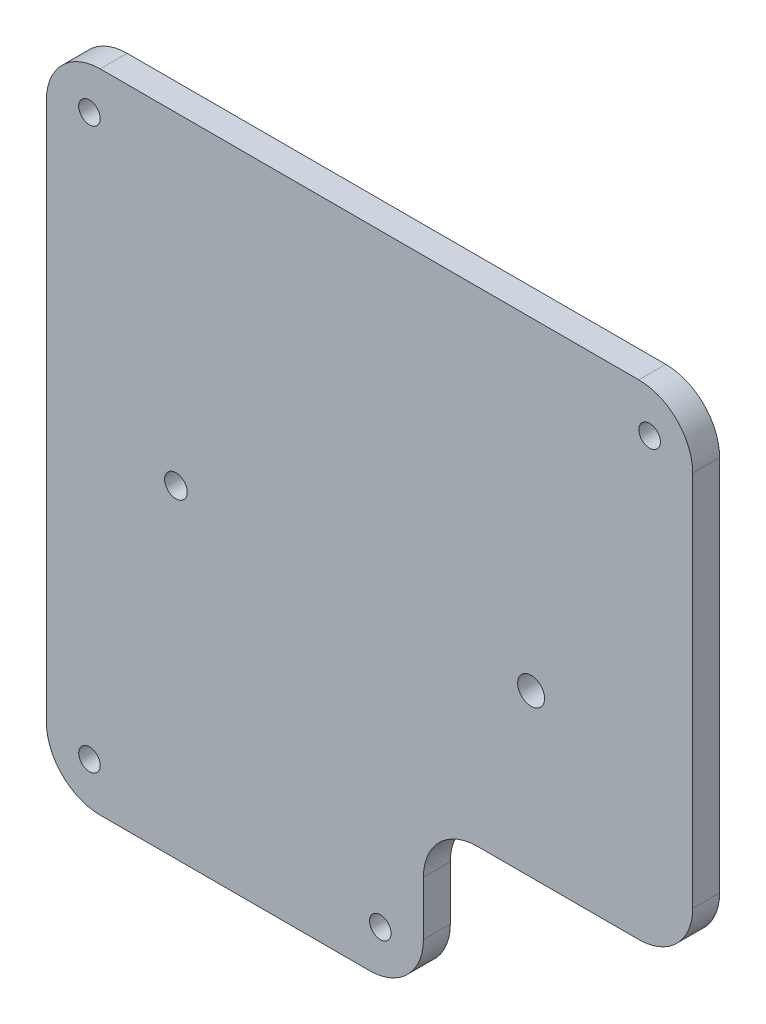
SolidWorks part; units mm, degrees
ref_plane "Alzado" through (0, 0, 0) normal (0, 0, 1) x (1, 0, 0)
ref_plane "Planta" through (0, 0, 0) normal (0, 1, 0) x (1, 0, 0)
ref_plane "Vista lateral" through (0, 0, 0) normal (1, 0, 0) x (0, 0, -1)
sketch "Croquis1" plane through (0, 0, 0) normal (0, 0, 1) x (1, 0, 0)
  line L0 (110, 30) -> (80, 30)
  line L1 (10, 0) -> (60, 0)
  line L2 (0, 10) -> (0, 110)
  line L3 (10, 120) -> (110, 120)
  line L4 (120, 40) -> (120, 110)
  line L5 (70, 20) -> (70, 10)
  arc A0 (10, 0) -> (0, 10) centre (10, 10) cw
  arc A1 (70, 10) -> (60, 0) centre (60, 10) cw
  arc A2 (110, 120) -> (120, 110) centre (110, 110) cw
  arc A3 (0, 110) -> (10, 120) centre (10, 110) cw
  arc A4 (80, 30) -> (70, 20) centre (80, 20) ccw
  arc A5 (110, 30) -> (120, 40) centre (110, 40) ccw
  point P7 (0, 0)
  point P10 (120, 0)
  point P15 (0, 120)
  dimension "D3" = 10
  dimension "D6" = 10
  dimension "D1" = 120
  dimension "D2" = 120
  dimension "D4" = 30
  dimension "D5" = 50
extrude "Saliente-Extruir1" add sketch "Croquis1" along normal blind 5
sketch "Croquis2" plane through (0, 0, 5) normal (0, 0, 1) x (1, 0, 0)
  line L0 (60, 120) -> (60, 75.4201) construction
  line L1 (110, 120) -> (10, 120) construction
  line L2 (0, 110) -> (0, 10) construction
  line L3 (0, 60) -> (90, 60) construction
  line L4 (120, 40) -> (120, 110) construction
  line L5 (70, 10) -> (70, 20) construction
  line L6 (10, 0) -> (60, 0) construction
  circle A0 centre (8, 112) radius 2
  circle A1 centre (8, 8) radius 2
  circle A2 centre (112, 8) radius 2
  circle A3 centre (112, 112) radius 2
  circle A4 centre (90, 60) radius 2.5
  circle A5 centre (62, 8) radius 2
  circle A6 centre (24.06, 60) radius 2.1
  point P23 (70, 15)
  dimension "D3" = 4
  dimension "D4" = 5
  dimension "D6" = 4
  dimension "D9" = 4.2
  dimension "D1" = 8
  dimension "D2" = 8
  dimension "D5" = 30
  dimension "D7" = 8
  dimension "D8" = 8
  dimension "D10" = 65.94
extrude "Cortar-Extruir1" cut sketch "Croquis2" against normal blind 10
